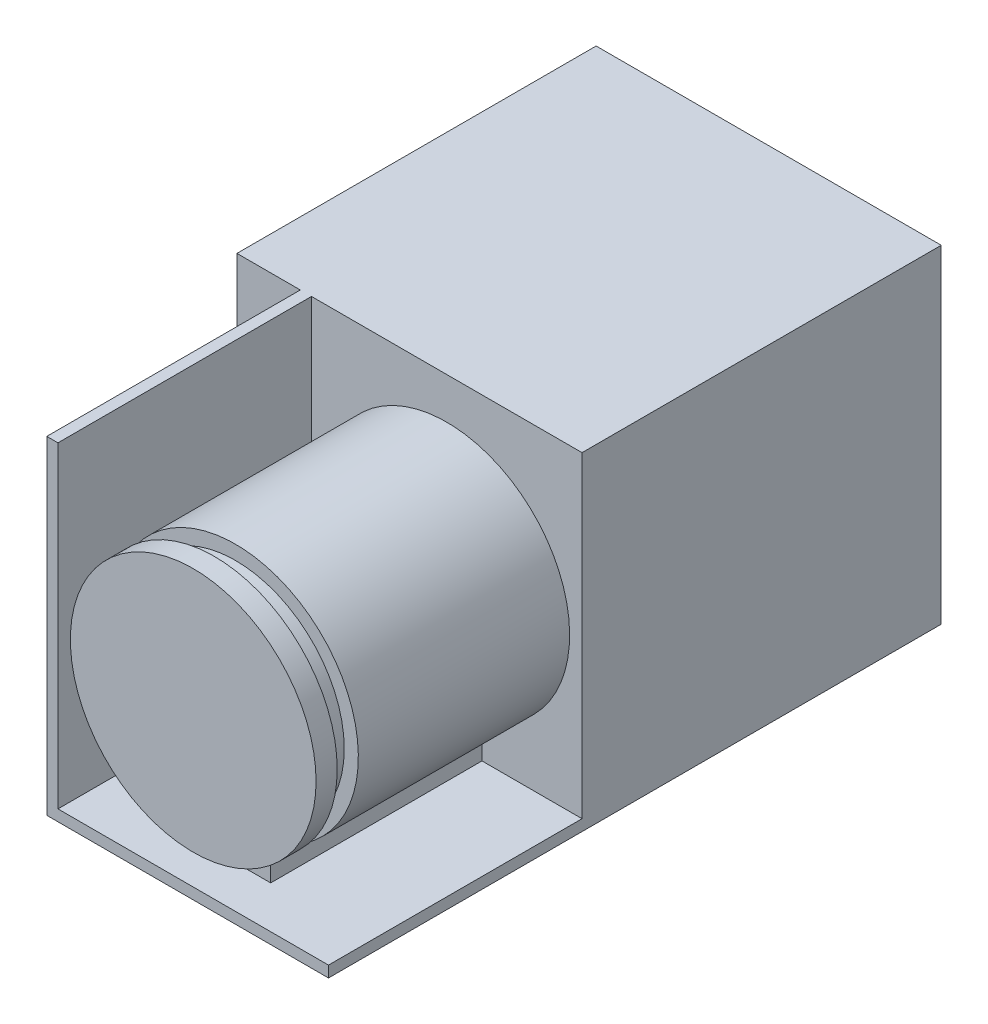
SolidWorks part; units mm, degrees
ref_plane "Front Plane" through (0, 0, 0) normal (0, 0, 1) x (1, 0, 0)
ref_plane "Top Plane" through (0, 0, 0) normal (0, 1, 0) x (1, 0, 0)
ref_plane "Right Plane" through (0, 0, 0) normal (1, 0, 0) x (0, 0, -1)
sketch "Sketch1" plane through (0, 0, 0) normal (0, 0, 1) x (1, 0, 0)
  line L1 (24.5, 23.3) -> (-24.5, 23.3)
  line L2 (24.5, 23.3) -> (24.5, -23.3)
  line L3 (24.5, -23.3) -> (-24.5, -23.3)
  line L4 (-24.5, 23.3) -> (-24.5, -23.3)
  line L5 (24.5, 23.3) -> (-24.5, -23.3) construction
  line L6 (24.5, -23.3) -> (-24.5, 23.3) construction
  point P0 (0, 0)
  dimension "D1" = 49
  dimension "D2" = 46.6
extrude "Boss-Extrude1" add sketch "Sketch1" along normal blind 51
sketch "Sketch2" plane through (0, 0, 51) normal (0, 0, 1) x (1, 0, 0)
  line L0 (24.5, -23.3) -> (24.5, -21.7125)
  line L1 (24.5, -23.3) -> (24.5, 23.3) construction
  line L2 (24.5, -21.7125) -> (-13.9125, -21.7125)
  line L3 (-13.9125, -21.7125) -> (-13.9125, 23.3)
  line L4 (24.5, 23.3) -> (-24.5, 23.3) construction
  line L5 (-13.9125, 23.3) -> (-15.5, 23.3)
  line L6 (-15.5, 23.3) -> (-15.5, -23.3)
  line L7 (-24.5, -23.3) -> (24.5, -23.3) construction
  line L8 (-15.5, -23.3) -> (24.5, -23.3)
  dimension "D1" = 40
  dimension "D2" = 1.5875
extrude "Boss-Extrude2" add sketch "Sketch2" along normal blind 36
sketch "Sketch3" plane through (0, 0, 51) normal (0, 0, 1) x (1, 0, 0)
  line L0 (0.2937, -21.7125) -> (0.2937, -16.7125)
  line L1 (24.5, -21.7125) -> (-13.9125, -21.7125) construction
  line L2 (0.2937, -21.7125) -> (10.2938, -21.7125)
  line L3 (24.5, -21.7125) -> (-13.9125, -21.7125) construction
  line L4 (10.2938, -21.7125) -> (10.2938, -16.7125)
  arc A0 (10.2938, -16.7125) -> (0.2937, -16.7125) centre (5.2938, 0) ccw
  point P6 (5.2938, -21.7125)
  dimension "D1" = 10
  dimension "D2" = 5
extrude "Boss-Extrude3" add sketch "Sketch3" along normal up to surface (36 mm away) up to face at (-1.6375, -7.2375, 87)
sketch "Sketch4" plane through (0, 0, 87) normal (0, 0, 1) x (1, 0, 0)
  circle A3 centre (5.2938, 0) radius 15.4444
  circle A4 centre (5.2938, 0) radius 17.4444
  arc A5 (10.2937, -16.7125) -> (0.2937, -16.7125) centre (5.2938, 0) ccw construction
  dimension "D1" = 2
extrude "Cut-Extrude1" cut sketch "Sketch4" against normal blind 3 from offset 3 offset against normal yes
sketch "Sketch5" plane through (0, 0, 87) normal (0, 0, 1) x (1, 0, 0)
  line L1 (0.2937, -21.7125) -> (10.2937, -21.7125)
  line L2 (0.2937, -21.7125) -> (0.2937, -16.7125)
  line L4 (10.2937, -21.7125) -> (10.2937, -16.7125)
  arc A0 (0.2937, -16.7125) -> (10.2937, -16.7125) centre (5.2938, 0) ccw
extrude "Cut-Extrude2" cut sketch "Sketch5" against normal up to surface (6 mm away)
